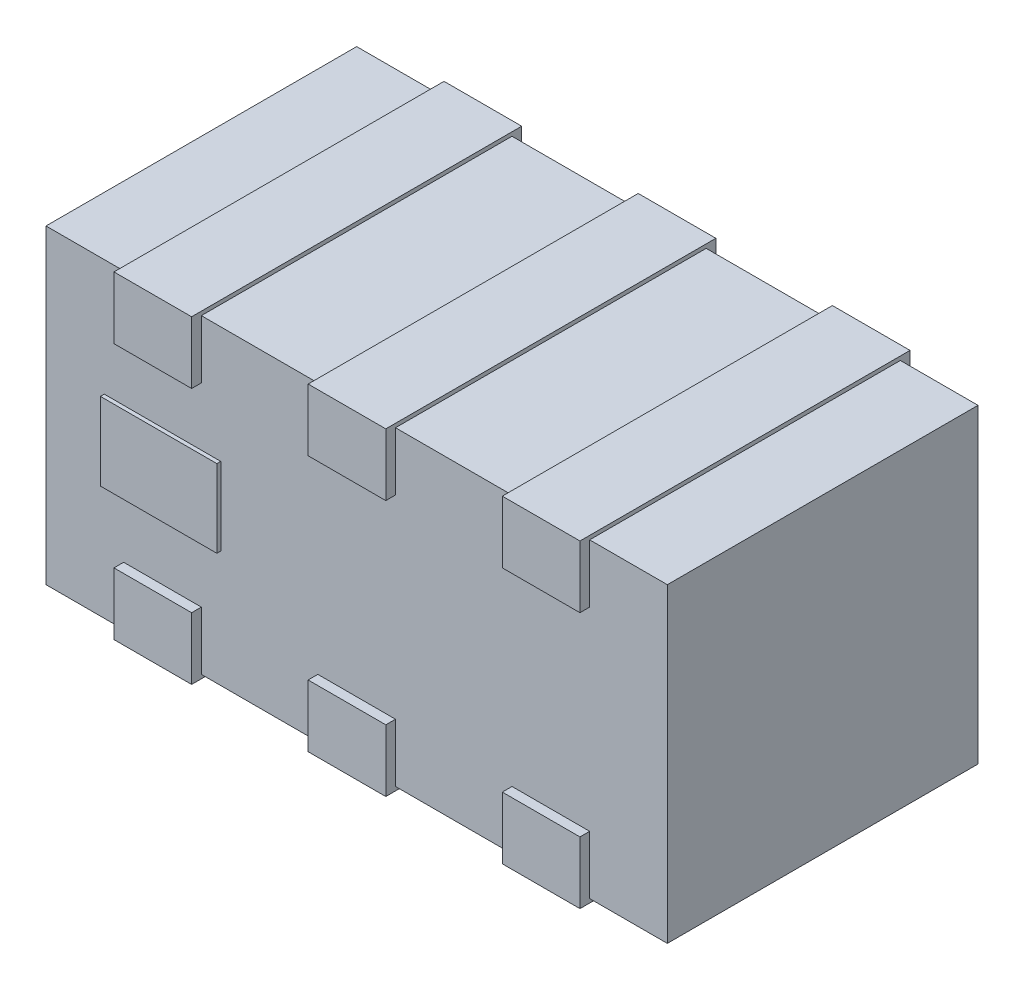
SolidWorks part; units mm, degrees
ref_plane "Спереди" through (0, 0, 0) normal (0, 0, 1) x (1, 0, 0)
ref_plane "Сверху" through (0, 0, 0) normal (0, 1, 0) x (1, 0, 0)
ref_plane "Справа" through (0, 0, 0) normal (1, 0, 0) x (0, 0, -1)
sketch "Эскиз1" plane through (0, 0, 0) normal (0, 1, 0) x (1, 0, 0)
  line L1 (-0.8, 0.4) -> (0.8, 0.4)
  line L2 (-0.8, 0.4) -> (-0.8, -0.4)
  line L3 (-0.8, -0.4) -> (0.8, -0.4)
  line L4 (0.8, 0.4) -> (0.8, -0.4)
  point P4 (0, 0.4)
  point P6 (-0.8, 0)
  dimension "D1" = 1.6
  dimension "D2" = 0.8
extrude "Бобышка-Вытянуть1" add sketch "Эскиз1" along normal blind 0.8
sketch "Эскиз2" plane through (0, 0.8, 0) normal (0, 1, 0) x (1, 0, 0)
  line L0 (0, 0.4) -> (0, -0.4) construction
  line L1 (-0.6, 0.425) -> (-0.4, 0.425)
  line L2 (-0.6, 0.425) -> (-0.6, -0.425)
  line L3 (-0.6, -0.425) -> (-0.4, -0.425)
  line L4 (-0.4, 0.425) -> (-0.4, -0.425)
  line L5 (-0.1, 0.425) -> (0.1, 0.425)
  line L6 (-0.1, 0.425) -> (-0.1, -0.425)
  line L7 (-0.1, -0.425) -> (0.1, -0.425)
  line L8 (0.1, 0.425) -> (0.1, -0.425)
  line L9 (0.4, 0.425) -> (0.6, 0.425)
  line L10 (0.4, 0.425) -> (0.4, -0.425)
  line L11 (0.4, -0.425) -> (0.6, -0.425)
  line L12 (0.6, 0.425) -> (0.6, -0.425)
  line L13 (0.8, 0.4) -> (-0.8, 0.4) construction
  line L14 (-0.8, -0.4) -> (0.8, -0.4) construction
  point P12 (0, 0.425)
  point P14 (-0.6, 0)
  point P15 (-0.1, 0)
  point P16 (0.4, 0)
  point P23 (0.6, 0)
  dimension "D1" = 0.2
  dimension "D2" = 0.3
  dimension "D3" = 0.85
extrude "Бобышка-Вытянуть2" add sketch "Эскиз2" along normal blind 0.16 from offset 0.15 offset against normal yes
sketch "Эскиз3" plane through (0, 0, 0) normal (0, -1, 0) x (1, 0, 0)
  line L1 (-0.6, 0.425) -> (-0.4, 0.425)
  line L2 (-0.6, 0.425) -> (-0.6, -0.425)
  line L3 (-0.6, -0.425) -> (-0.4, -0.425)
  line L4 (-0.4, 0.425) -> (-0.4, -0.425)
  line L5 (-0.1, 0.425) -> (0.1, 0.425)
  line L6 (-0.1, 0.425) -> (-0.1, -0.425)
  line L7 (-0.1, -0.425) -> (0.1, -0.425)
  line L8 (0.1, 0.425) -> (0.1, -0.425)
  line L9 (0.4, 0.425) -> (0.6, 0.425)
  line L10 (0.4, 0.425) -> (0.4, -0.425)
  line L11 (0.4, -0.425) -> (0.6, -0.425)
  line L12 (0.6, 0.425) -> (0.6, -0.425)
extrude "Бобышка-Вытянуть3" add sketch "Эскиз3" along normal blind 0.16 from offset 0.15 offset against normal yes
sketch "Эскиз4" plane through (0, 0, 0.4) normal (0, 0, 1) x (1, 0, 0)
  line L0 (-0.8, 0.8) -> (-0.8, 0) construction
  line L1 (-0.65, 0.5) -> (-0.35, 0.5)
  line L2 (-0.65, 0.5) -> (-0.65, 0.3)
  line L3 (-0.65, 0.3) -> (-0.35, 0.3)
  line L4 (-0.35, 0.5) -> (-0.35, 0.3)
  line L5 (-0.6, 0.65) -> (-0.4, 0.65) construction
  point P4 (-0.65, 0.4)
  point P7 (-0.8, 0.4)
  point P8 (-0.5, 0.5)
  point P11 (-0.5, 0.65)
  dimension "D1" = 0.2
  dimension "D2" = 0.3
extrude "Бобышка-Вытянуть4" add sketch "Эскиз4" along normal blind 0.01
